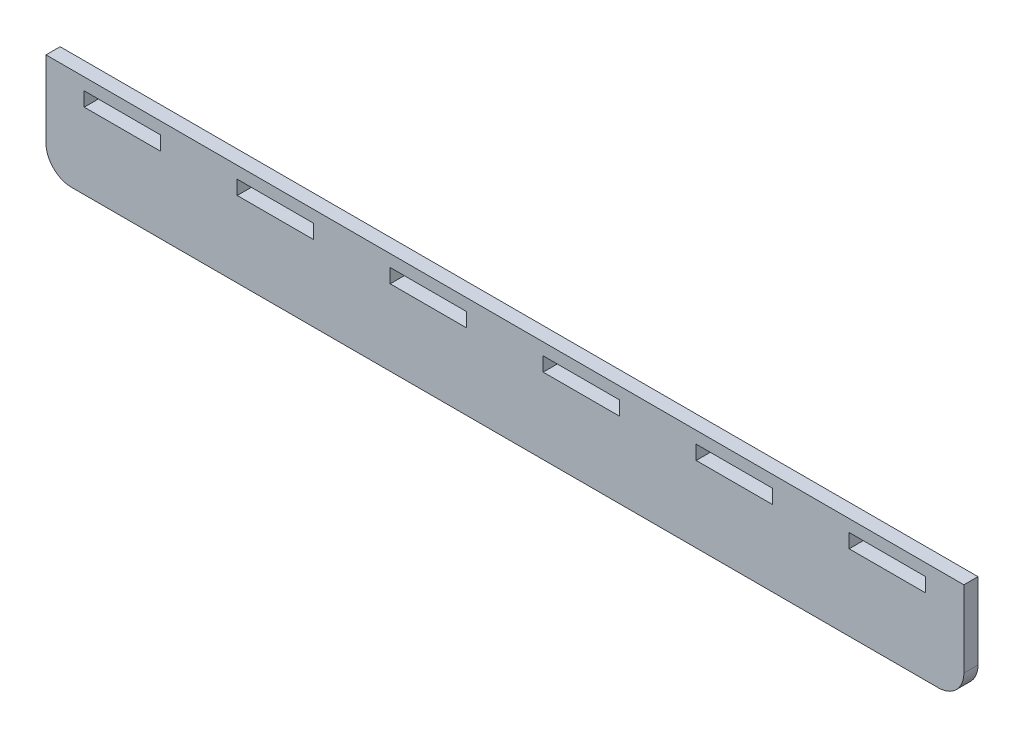
SolidWorks part; units mm, degrees
ref_plane "Front Plane" through (0, 0, 0) normal (0, 0, 1) x (1, 0, 0)
ref_plane "Top Plane" through (0, 0, 0) normal (0, 1, 0) x (1, 0, 0)
ref_plane "Right Plane" through (0, 0, 0) normal (1, 0, 0) x (0, 0, -1)
sketch "Sketch2" plane through (0, 0, 0) normal (0, 0, 1) x (1, 0, 0)
  line L5 (34.1639, 15.146) -> (119.4339, 15.146)
  line L35 (59.4746, 0.146) -> (59.4746, 15.146)
  line L40 (34.2026, 0.146) -> (111.5343, 0.146)
  line L57 (29.4339, 10.416) -> (34.1639, 15.146)
  line L58 (29.4746, 4.876) -> (34.2026, 0.146)
  line L62 (74.4746, 10.416) -> (74.4746, 4.876)
  line L63 (74.4746, 10.416) -> (104.4746, 10.416)
  line L64 (104.4746, 10.416) -> (104.4746, 4.876)
  line L65 (74.4746, 4.876) -> (104.4746, 4.876)
  line L66 (314.4746, 10.416) -> (314.4746, 4.876)
  line L67 (29.4746, 4.876) -> (44.4746, 4.876)
  line L69 (29.4339, 10.416) -> (44.4746, 10.416)
  line L70 (44.4746, 4.876) -> (44.4746, 10.416)
  line L75 (59.4746, 0.146) -> (419.4746, 0.146)
  line L76 (134.4746, 10.416) -> (134.4746, 4.876)
  line L77 (134.4746, 4.876) -> (164.4746, 4.876)
  line L78 (164.4746, 10.416) -> (164.4746, 4.876)
  line L79 (134.4746, 10.416) -> (164.4746, 10.416)
  line L80 (194.4746, 10.416) -> (194.4746, 4.876)
  line L81 (194.4746, 4.876) -> (224.4746, 4.876)
  line L82 (224.4746, 10.416) -> (224.4746, 4.876)
  line L83 (194.4746, 10.416) -> (224.4746, 10.416)
  line L84 (254.4746, 10.416) -> (254.4746, 4.876)
  line L85 (254.4746, 4.876) -> (284.4746, 4.876)
  line L86 (284.4746, 10.416) -> (284.4746, 4.876)
  line L87 (254.4746, 10.416) -> (284.4746, 10.416)
  line L88 (239.4746, 45.3214) -> (239.4746, -24.4893) construction
  line L89 (224.4746, 10.416) -> (254.4746, 10.416) construction
  line L90 (59.4746, 0.146) -> (59.4746, -24.854)
  line L91 (434.4746, 4.876) -> (434.4746, 10.416)
  line L92 (449.5153, 10.416) -> (434.4746, 10.416)
  line L93 (449.4746, 4.876) -> (434.4746, 4.876)
  line L94 (59.4746, -24.854) -> (419.4746, -24.854)
  line L95 (449.4746, 4.876) -> (444.7466, 0.146)
  line L96 (449.5153, 10.416) -> (444.7853, 15.146)
  line L97 (444.7466, 0.146) -> (367.4149, 0.146)
  line L98 (444.7853, 15.146) -> (359.5153, 15.146)
  line L99 (119.4339, 15.146) -> (359.5153, 15.146)
  line L100 (111.5343, 0.146) -> (367.4149, 0.146)
  line L101 (419.4746, 0.146) -> (419.4746, -24.854)
  line L102 (314.4746, 4.876) -> (344.4746, 4.876)
  line L103 (344.4746, 10.416) -> (344.4746, 4.876)
  line L104 (314.4746, 10.416) -> (344.4746, 10.416)
  line L105 (374.4746, 10.416) -> (374.4746, 4.876)
  line L106 (374.4746, 4.876) -> (404.4746, 4.876)
  line L107 (404.4746, 10.416) -> (404.4746, 4.876)
  line L108 (374.4746, 10.416) -> (404.4746, 10.416)
  line L109 (419.4746, 0.146) -> (419.4746, 15.146)
  point P0 (29.4339, 15.146)
  point P2 (29.4726, 0.146)
  point P30 (239.4746, 10.416)
  point P31 (449.4766, 0.146)
  point P32 (449.5153, 15.146)
  dimension "D2" = 15
  dimension "D3" = 6
  dimension "D4" = 25
  dimension "D5" = 15
  dimension "D6" = 15
  dimension "D8" = 30
  dimension "D9" = 30
  dimension "D10" = 5.54
  dimension "D11" = 30
  dimension "D7" = 15
extrude "Boss-Extrude1" add sketch "Sketch2" along normal blind 5.54 contours L99 L5 L57 L69 L70 L67 L58 L40 L75 L97 L95 L93 L91 L92 L96 L98 L65 L62 L63 L64 L76 L79 L78 L77 L80 L83 L82 L81 L84 L87 L86 L85 | L101 L75 L40 L90 L94
fillet "Fillet1" radius 10 2 edges at (419.4746, -24.854, 2.77) (59.4746, -24.854, 2.77)
